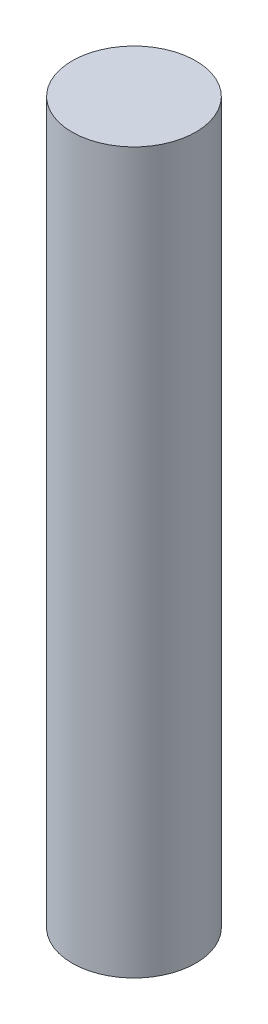
SolidWorks part; units mm, degrees
ref_plane "Front Plane" through (0, 0, 0) normal (0, 0, 1) x (1, 0, 0)
ref_plane "Top Plane" through (0, 0, 0) normal (0, 1, 0) x (1, 0, 0)
ref_plane "Right Plane" through (0, 0, 0) normal (1, 0, 0) x (0, 0, -1)
sketch "Sketch1" plane through (0, 0, 0) normal (0, 1, 0) x (1, 0, 0)
  circle A0 centre (0, 0) radius 3.6805
  dimension "D1" = 7.3609
extrude "Boss-Extrude1" add sketch "Sketch1" along normal blind 42.8625
